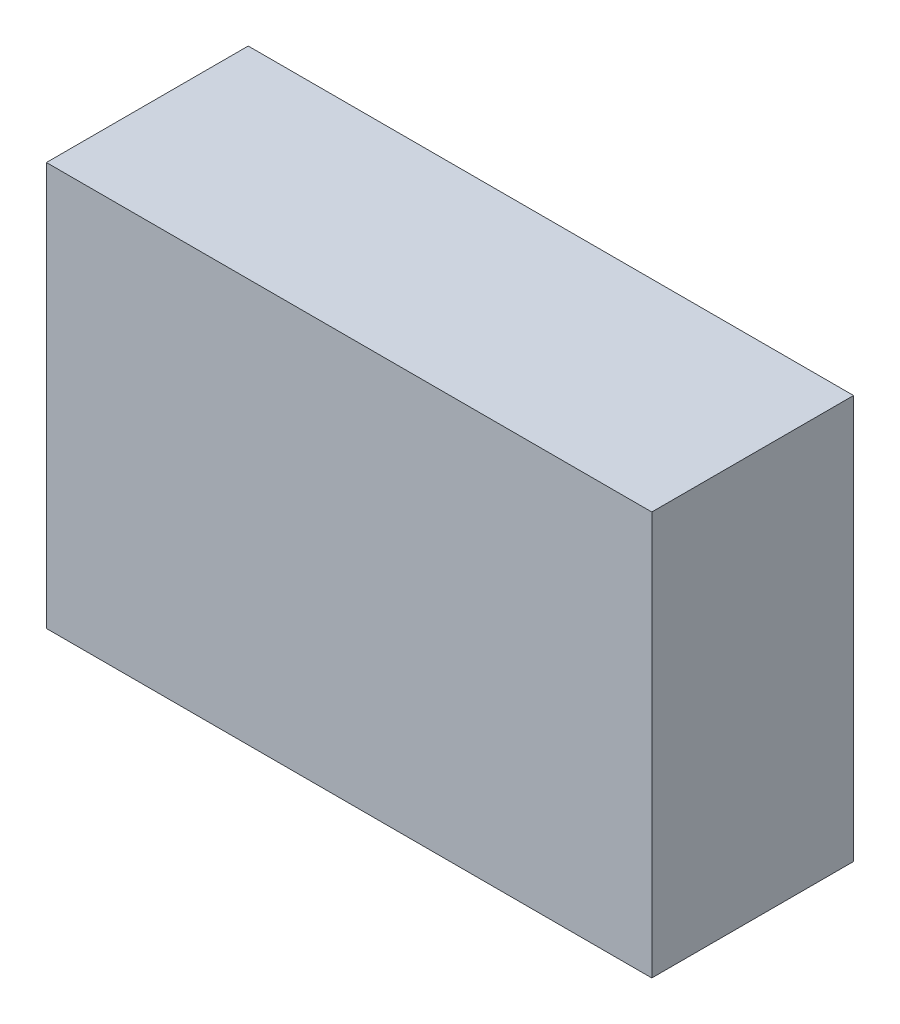
SolidWorks part; units mm, degrees
ref_plane "Front Plane" through (0, 0, 0) normal (0, 0, 1) x (1, 0, 0)
ref_plane "Top Plane" through (0, 0, 0) normal (0, 1, 0) x (1, 0, 0)
ref_plane "Right Plane" through (0, 0, 0) normal (1, 0, 0) x (0, 0, -1)
sketch "Sketch1" plane through (0, 0, 0) normal (0, 0, 1) x (1, 0, 0)
  line L1 (0, 0) -> (152.4, 0)
  line L2 (0, 0) -> (0, 101.6)
  line L3 (0, 101.6) -> (152.4, 101.6)
  line L4 (152.4, 0) -> (152.4, 101.6)
  dimension "D1" = 152.4
  dimension "D2" = 101.6
extrude "Boss-Extrude1" add sketch "Sketch1" along normal mid plane 50.8
